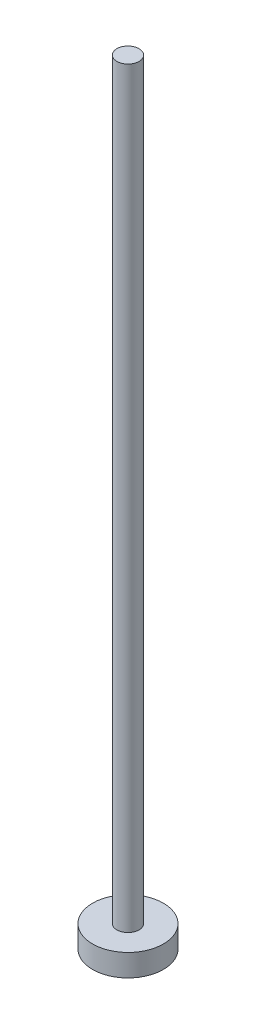
SolidWorks part; units mm, degrees
ref_plane "Płaszczyzna przednia" through (0, 0, 0) normal (0, 0, 1) x (1, 0, 0)
ref_plane "Płaszczyzna górna" through (0, 0, 0) normal (0, 1, 0) x (1, 0, 0)
ref_plane "Płaszczyzna prawa" through (0, 0, 0) normal (1, 0, 0) x (0, 0, -1)
sketch "Szkic1" plane through (0, 0, 0) normal (0, 0, 1) x (1, 0, 0)
  line L0 (0, 175) -> (0, 0)
  line L1 (0, 0) -> (8, 0)
  line L2 (8, 0) -> (8, 5)
  line L3 (8, 5) -> (2.5, 5)
  line L4 (2.5, 5) -> (2.5, 175)
  line L5 (2.5, 175) -> (0, 175)
  dimension "D1" = 8
  dimension "D2" = 5
  dimension "D3" = 170
  dimension "D4" = 2.5
revolve "Obrót1" add sketch "Szkic1" angle 360 about L0
